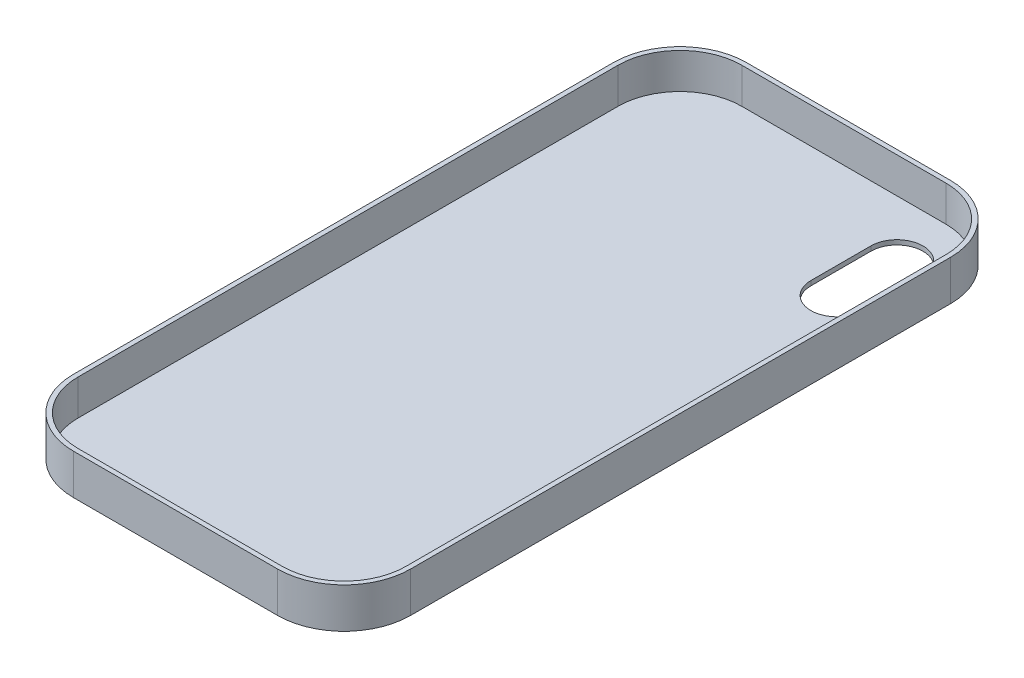
SolidWorks part; units mm, degrees
ref_plane "Front Plane" through (0, 0, 0) normal (0, 0, 1) x (1, 0, 0)
ref_plane "Top Plane" through (0, 0, 0) normal (0, 1, 0) x (1, 0, 0)
ref_plane "Right Plane" through (0, 0, 0) normal (1, 0, 0) x (0, 0, -1)
sketch "Sketch1" plane through (0, 0, 0) normal (0, 1, 0) x (1, 0, 0)
  line L1 (-22.08, -72.785) -> (22.08, -72.785)
  line L2 (-36.47, -58.395) -> (-36.47, 58.395)
  line L3 (-22.08, 72.785) -> (22.08, 72.785)
  line L4 (36.47, -58.395) -> (36.47, 58.395)
  line L5 (-36.47, -72.785) -> (36.47, 72.785) construction
  line L6 (-36.47, 72.785) -> (36.47, -72.785) construction
  arc A0 (22.08, -72.785) -> (36.47, -58.395) centre (22.08, -58.395) ccw
  arc A1 (-22.08, -72.785) -> (-36.47, -58.395) centre (-22.08, -58.395) cw
  arc A2 (22.08, 72.785) -> (36.47, 58.395) centre (22.08, 58.395) cw
  arc A3 (-36.47, 58.395) -> (-22.08, 72.785) centre (-22.08, 58.395) cw
  point P0 (0, 0)
  dimension "D3" = 14.39
  dimension "D1" = 145.57
  dimension "D2" = 72.94
extrude "Boss-Extrude1" add sketch "Sketch1" along normal blind 8.7
sketch "Sketch2" plane through (0, 8.7, 0) normal (0, 1, 0) x (1, 0, 0)
  line L8 (-22.08, -71.785) -> (22.08, -71.785)
  line L9 (-35.47, 58.395) -> (-35.47, -58.395)
  line L10 (22.08, 71.785) -> (-22.08, 71.785)
  line L11 (35.47, -58.395) -> (35.47, 58.395)
  line L12 (-22.08, -71.785) -> (22.08, -71.785)
  line L13 (-35.47, 58.395) -> (-35.47, -58.395)
  line L14 (22.08, 71.785) -> (-22.08, 71.785)
  line L15 (35.47, -58.395) -> (35.47, 58.395)
  arc A8 (22.08, -71.785) -> (35.47, -58.395) centre (22.08, -58.395) ccw
  arc A9 (-35.47, -58.395) -> (-22.08, -71.785) centre (-22.08, -58.395) ccw
  arc A10 (-22.08, 71.785) -> (-35.47, 58.395) centre (-22.08, 58.395) ccw
  arc A11 (35.47, 58.395) -> (22.08, 71.785) centre (22.08, 58.395) ccw
  arc A12 (22.08, -71.785) -> (35.47, -58.395) centre (22.08, -58.395) ccw
  arc A13 (-35.47, -58.395) -> (-22.08, -71.785) centre (-22.08, -58.395) ccw
  arc A14 (-22.08, 71.785) -> (-35.47, 58.395) centre (-22.08, 58.395) ccw
  arc A15 (35.47, 58.395) -> (22.08, 71.785) centre (22.08, 58.395) ccw
  dimension "D1" = 1
extrude "Cut-Extrude1" cut sketch "Sketch2" against normal blind 7.7
sketch "Sketch3" plane through (0, 1, 0) normal (0, 1, 0) x (1, 0, 0)
  line L0 (23.65, 59.6) -> (23.65, 46.63) construction
  line L1 (29.28, 59.6) -> (29.28, 46.63)
  line L2 (18.02, 59.6) -> (18.02, 46.63)
  line L3 (35.47, -58.395) -> (35.47, 58.395) construction
  line L6 (22.08, 71.785) -> (-22.08, 71.785) construction
  arc A0 (29.28, 59.6) -> (18.02, 59.6) centre (23.65, 59.6) ccw
  arc A1 (18.02, 46.63) -> (29.28, 46.63) centre (23.65, 46.63) ccw
  point P2 (23.65, 53.115)
  point P7 (23.65, 65.23)
  point P8 (23.65, 41)
  dimension "D2" = 24.23
  dimension "D1" = 11.26
  dimension "D3" = 11.82
  dimension "D4" = 18.67
extrude "Cut-Extrude2" cut sketch "Sketch3" against normal through all
